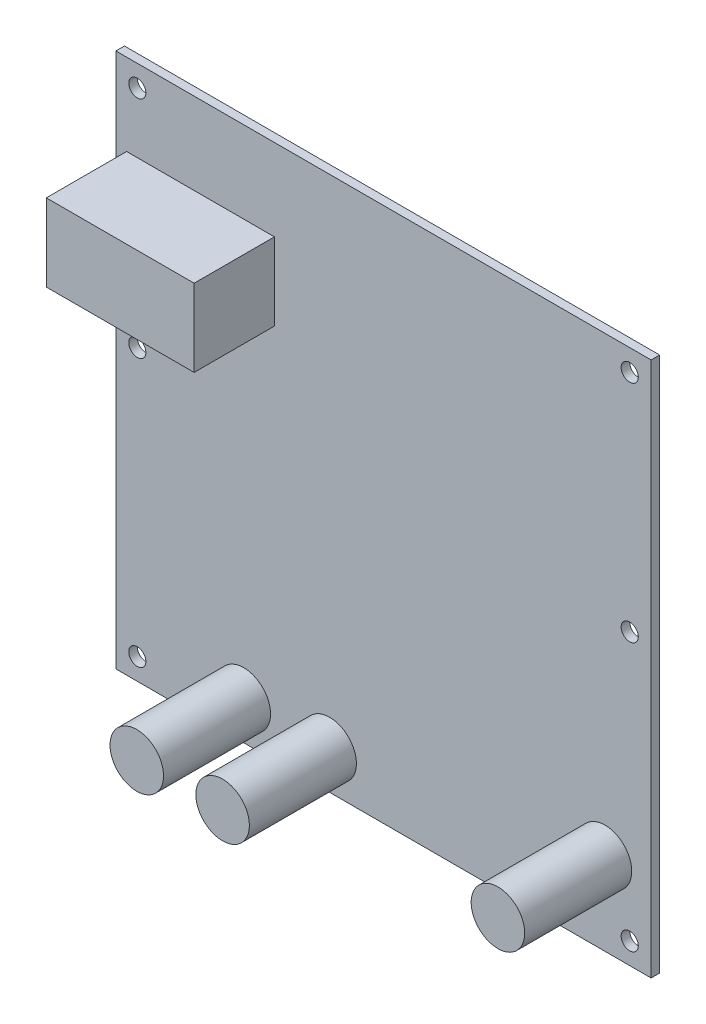
SolidWorks part; units mm, degrees
ref_plane "Plan de face" through (0, 0, 0) normal (0, 0, 1) x (1, 0, 0)
ref_plane "Plan de dessus" through (0, 0, 0) normal (0, 1, 0) x (1, 0, 0)
ref_plane "Plan de droite" through (0, 0, 0) normal (1, 0, 0) x (0, 0, -1)
sketch "Esquisse1" plane through (0, 0, 0) normal (0, 0, 1) x (1, 0, 0)
  line L0 (-46, 46) -> (46, -46) construction
  line L1 (-50, 50) -> (50, 50)
  line L2 (-50, 50) -> (-50, -50)
  line L3 (-50, -50) -> (50, -50)
  line L4 (50, 50) -> (50, -50)
  circle A0 centre (-46, 46) radius 1.6
  circle A1 centre (46, 46) radius 1.6
  circle A2 centre (46, 4) radius 1.6
  circle A3 centre (-46, 4) radius 1.6
  circle A4 centre (-46, -46) radius 1.6
  circle A5 centre (46, -46) radius 1.6
  point P4 (0, 50)
  point P7 (50, 0)
  point P20 (0, 0)
  dimension "D3" = 3.2
  dimension "D1" = 100
  dimension "D2" = 100
  dimension "D4" = 92
  dimension "D5" = 92
  dimension "D6" = 42
extrude "Boss.-Extru.1" add sketch "Esquisse1" along normal blind 1.6
sketch "Esquisse2" plane through (0, 0, 1.6) normal (0, 0, 1) x (1, 0, 0)
  circle A0 centre (-26.0991, -42.8429) radius 5
  circle A1 centre (-10.0631, -42.8429) radius 5
  circle A2 centre (41.3767, -34.5637) radius 5
  point P6 (0, 0)
  point P7 (-10.0631, -42.8429)
  point P8 (41.3767, -34.5637)
  dimension "D1" = 10
extrude "Boss.-Extru.2" add sketch "Esquisse2" along normal blind 20
sketch "Esquisse3" plane through (0, 0, 1.6) normal (0, 0, 1) x (1, 0, 0)
  line L1 (-48.0009, 34.7306) -> (-20.3817, 34.7306)
  line L2 (-48.0009, 34.7306) -> (-48.0009, 20.2937)
  line L3 (-48.0009, 20.2937) -> (-20.3817, 20.2937)
  line L4 (-20.3817, 34.7306) -> (-20.3817, 20.2937)
extrude "Boss.-Extru.3" add sketch "Esquisse3" along normal blind 15
